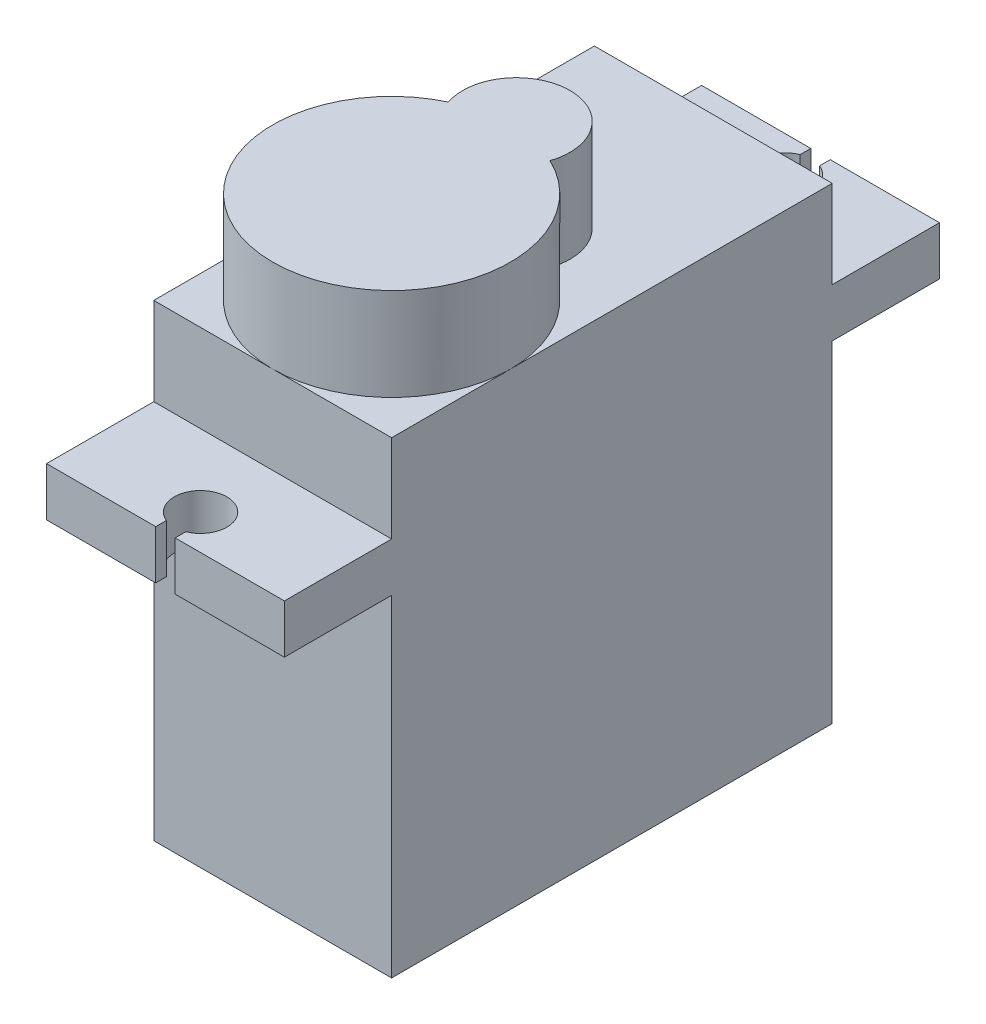
SolidWorks part; units mm, degrees
ref_plane "Front Plane" through (0, 0, 0) normal (0, 0, 1) x (1, 0, 0)
ref_plane "Top Plane" through (0, 0, 0) normal (0, 1, 0) x (1, 0, 0)
ref_plane "Right Plane" through (0, 0, 0) normal (1, 0, 0) x (0, 0, -1)
sketch "Sketch1" plane through (0, 0, 0) normal (0, 1, 0) x (1, 0, 0)
  line L1 (0, 0) -> (12.2, 0)
  line L2 (0, 0) -> (0, 22.6)
  line L3 (0, 22.6) -> (12.2, 22.6)
  line L4 (12.2, 0) -> (12.2, 22.6)
  dimension "D1" = 12.2
  dimension "D2" = 22.6
extrude "Boss-Extrude1" add sketch "Sketch1" along normal blind 24
ref_plane "Plane1" through (0, 19.5, 0) normal (0, 1, 0) x (1, 0, 0)
sketch "Sketch2" plane through (0, 19.5, 0) normal (0, 1, 0) x (1, 0, 0)
  line L0 (12.2, 0) -> (12.2, 22.6) construction
  line L1 (0, 22.6) -> (12.2, 22.6)
  line L2 (0, 22.6) -> (0, 28.1)
  line L4 (12.2, 22.6) -> (12.2, 28.1)
  line L5 (5.6, 27.554) -> (5.6, 28.1)
  line L6 (6.6, 27.554) -> (6.6, 28.1)
  line L7 (5.6, 27.554) -> (6.6, 27.554) construction
  line L8 (0, 28.1) -> (5.6, 28.1)
  line L9 (6.6, 28.1) -> (12.2, 28.1)
  arc A1 (5.6, 27.554) -> (6.6, 27.554) centre (6.1, 26.3) ccw
  point P10 (8.0723, 28.1)
  point P13 (6.1, 22.6)
  point P14 (6.6, 30.2858)
  dimension "D2" = 1.35
  dimension "D1" = 5.5
  dimension "D3" = 1.8
  dimension "1" = 1
extrude "Boss-Extrude2" add sketch "Sketch2" against normal blind 2.5
ref_plane "Plane2" through (0, 0, -11.3) normal (0, 0, 1) x (1, 0, 0)
mirror "Mirror1" about plane through (0, 0, -11.3) normal (0, 0, 1) of "Boss-Extrude2"
ref_plane "Plane3" through (6.1, 0, 0) normal (-1, 0, 0) x (0, 0, 1)
sketch "Sketch6" plane through (0, 24, 0) normal (0, 1, 0) x (1, 0, 0)
  line L0 (6.1, 13.2) -> (6.1, -13.2) construction
  line L1 (0, 0) -> (12.2, 0) construction
  line L2 (12.2, 0) -> (12.2, 22.6) construction
  line L3 (0, 22.6) -> (0, 0) construction
  line L4 (0, 0) -> (12.2, 0) construction
  arc A0 (8.7041, 11.6162) -> (3.4959, 11.6162) centre (6.1, 6.1) cw
  arc A1 (3.4959, 11.6162) -> (8.7041, 11.6162) centre (6.1, 12.5) cw
  point P6 (11.1367, 11.7457)
  point P10 (4.1942, 10.1519)
  point P16 (3.4085, 11.5741)
  dimension "D2" = 2.75
  dimension "D1" = 12.5
extrude "Boss-Extrude3" add sketch "Sketch6" along normal blind 4.75
